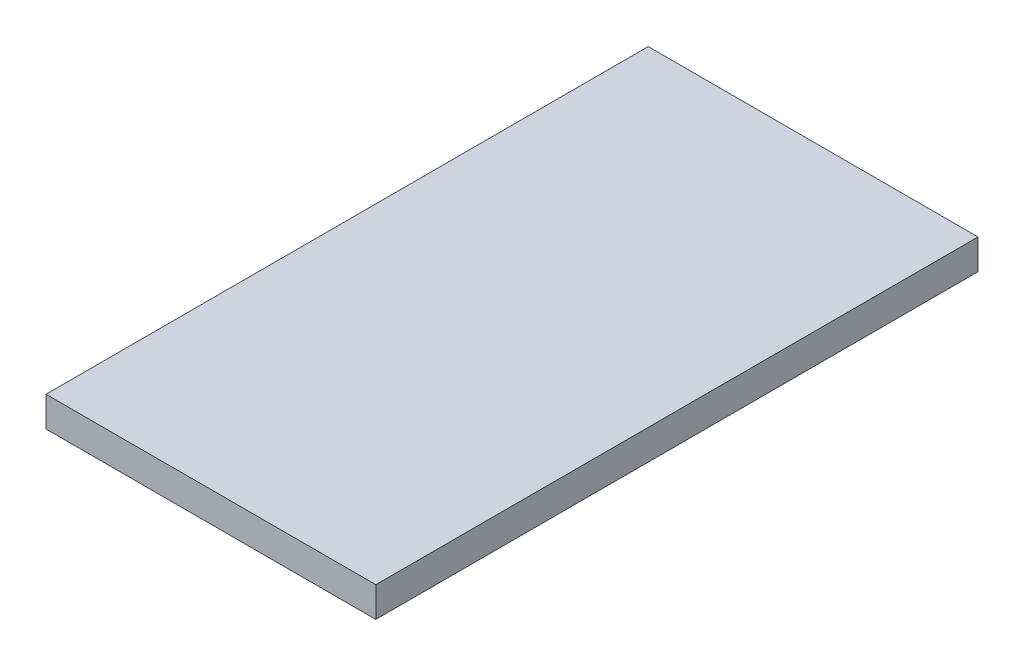
SolidWorks part; units mm, degrees
ref_plane "Front Plane" through (0, 0, 0) normal (0, 0, 1) x (1, 0, 0)
ref_plane "Top Plane" through (0, 0, 0) normal (0, 1, 0) x (1, 0, 0)
ref_plane "Right Plane" through (0, 0, 0) normal (1, 0, 0) x (0, 0, -1)
sketch "Sketch1" plane through (0, 0, 0) normal (0, 1, 0) x (1, 0, 0)
  line L1 (11.5, 21) -> (-11.5, 21)
  line L2 (11.5, 21) -> (11.5, -21)
  line L3 (11.5, -21) -> (-11.5, -21)
  line L4 (-11.5, 21) -> (-11.5, -21)
  line L5 (11.5, 21) -> (-11.5, -21) construction
  line L6 (11.5, -21) -> (-11.5, 21) construction
  point P0 (0, 0)
  dimension "D1" = 42
  dimension "D2" = 23
extrude "Boss-Extrude2" add sketch "Sketch1" along normal blind 2.1
